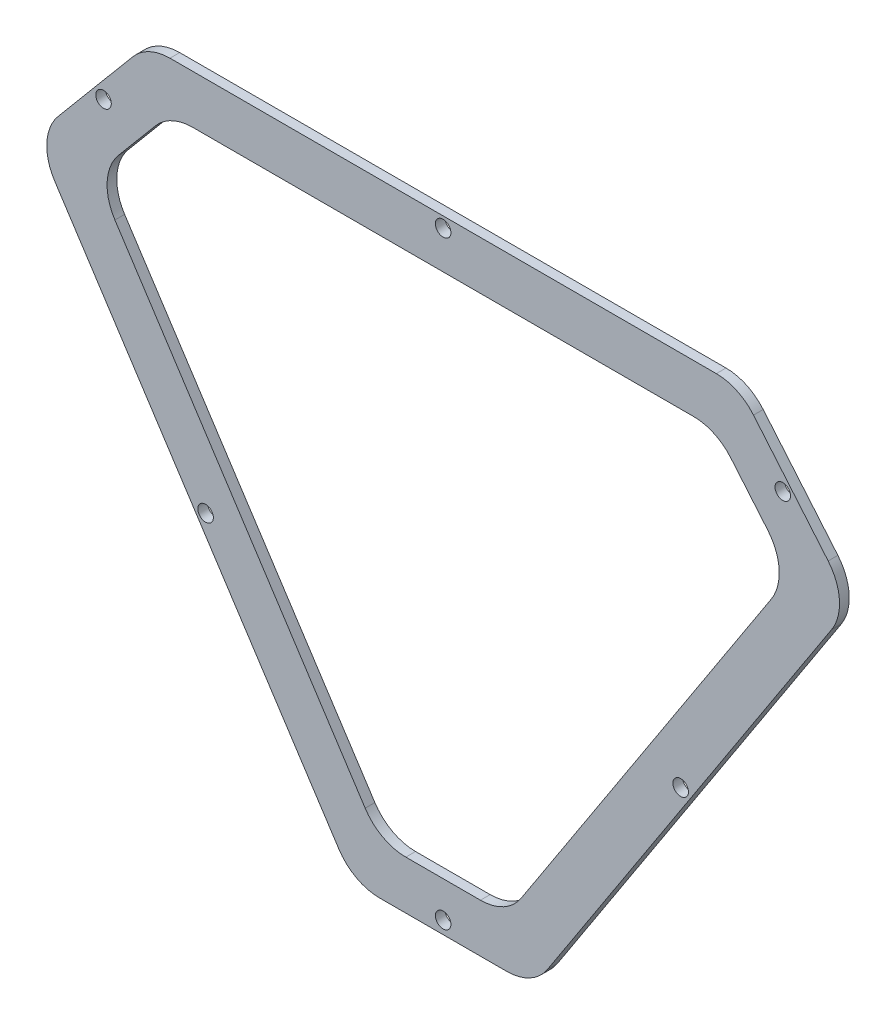
SolidWorks part; units mm, degrees
ref_plane "Plan de face" through (0, 0, 0) normal (0, 0, 1) x (1, 0, 0)
ref_plane "Plan de dessus" through (0, 0, 0) normal (0, 1, 0) x (1, 0, 0)
ref_plane "Plan de droite" through (0, 0, 0) normal (1, 0, 0) x (0, 0, -1)
sketch "Esquisse1" plane through (0, 0, 0) normal (0, 0, 1) x (1, 0, 0)
  line L0 (-40.8796, 34.6157) -> (81.0428, 34.6157)
  line L1 (81.0428, 34.6157) -> (104.1935, 7.0258)
  line L2 (104.1935, 7.0258) -> (38.618, -93.6745)
  line L3 (38.618, -93.6745) -> (1.5452, -93.6745)
  line L4 (1.5452, -93.6745) -> (-64.0303, 7.0258)
  line L5 (-64.0303, 7.0258) -> (-40.8796, 34.6157)
  line L6 (101.9984, 11.6642) -> (84.0469, 33.058) construction
  line L7 (-38.6879, 29.9157) -> (-58.1914, 6.6723) construction
  line L8 (-58.1914, 6.6723) -> (3.5509, -88.1416) construction
  line L10 (-44.0168, 31.3436) -> (-59.6403, 12.7242) construction
  line L12 (-60.3598, 0.8394) -> (-1.5758, -89.4315) construction
  line L13 (76.5196, 34.9157) -> (-36.3564, 34.9157) construction
  line L14 (99.8036, 12.7242) -> (84.1801, 31.3436) construction
  line L15 (41.7391, -89.4315) -> (100.523, 0.8394) construction
  line L16 (6.804, -93.9745) -> (33.3592, -93.9745) construction
  dimension "D1" = 0.3
  dimension "D2" = 0.3
  dimension "D3" = 0.3
  dimension "D4" = 0.3
  dimension "D5" = 0.3
  dimension "D6" = 0.3
extrude "Boss.-Extru.1" add sketch "Esquisse1" along normal blind 2
fillet "Congé1" radius 10 6 edges at (-40.8796, 34.6157, 1) (-64.0303, 7.0258, 1) (1.5452, -93.6745, 1) (38.618, -93.6745, 1) (104.1935, 7.0258, 1) (81.0428, 34.6157, 1)
sketch "Esquisse2" plane through (0, 0, 2) normal (0, 0, 1) x (1, 0, 0)
  line L0 (-36.2165, 24.6157) -> (-51.6072, 6.2738)
  line L1 (-51.6072, 6.2738) -> (6.9667, -83.6745)
  line L2 (6.9667, -83.6745) -> (33.1965, -83.6745)
  line L3 (-36.2165, 24.6157) -> (76.3797, 24.6157)
  line L4 (20.0816, 24.6157) -> (20.0816, -83.6745) construction
  line L5 (-59.9871, 0.8169) -> (-1.4132, -89.1315) construction
  line L6 (-43.8769, 31.0436) -> (-59.2676, 12.7017) construction
  line L7 (76.3797, 34.6157) -> (-36.2165, 34.6157) construction
  line L8 (6.9667, -93.6745) -> (33.1965, -93.6745) construction
  line L9 (91.7704, 6.2738) -> (33.1965, -83.6745)
  line L10 (76.3797, 24.6157) -> (91.7704, 6.2738)
  line L13 (41.5764, -89.1315) -> (100.1503, 0.8169) construction
  dimension "D1" = 10
  dimension "D2" = 10
  dimension "D3" = 10
  dimension "D4" = 10
extrude "Enlèv. mat.-Extru.1" cut sketch "Esquisse2" against normal blind 2
fillet "Congé2" radius 10 6 edges at (76.3797, 24.6157, 1) (91.7704, 6.2738, 1) (33.1965, -83.6745, 1) (6.9667, -83.6745, 1) (-36.2165, 24.6157, 1) (-51.6072, 6.2738, 1)
sketch "Esquisse3" plane through (0, 0, 2) normal (0, 0, 1) x (1, 0, 0)
  circle A1 centre (20.0816, -91.0581) radius 1.6
  circle A2 centre (-28.8728, -42.9318) radius 1.6
  circle A3 centre (20.0816, 32.4157) radius 1.6
  circle A4 centre (90.0767, 20.4269) radius 1.6
  circle A5 centre (69.0361, -42.9318) radius 1.6
  circle A6 centre (-49.9135, 20.4269) radius 1.6
  dimension "D1" = 3.2
extrude "Enlèv. mat.-Extru.2" cut sketch "Esquisse3" against normal blind 10
